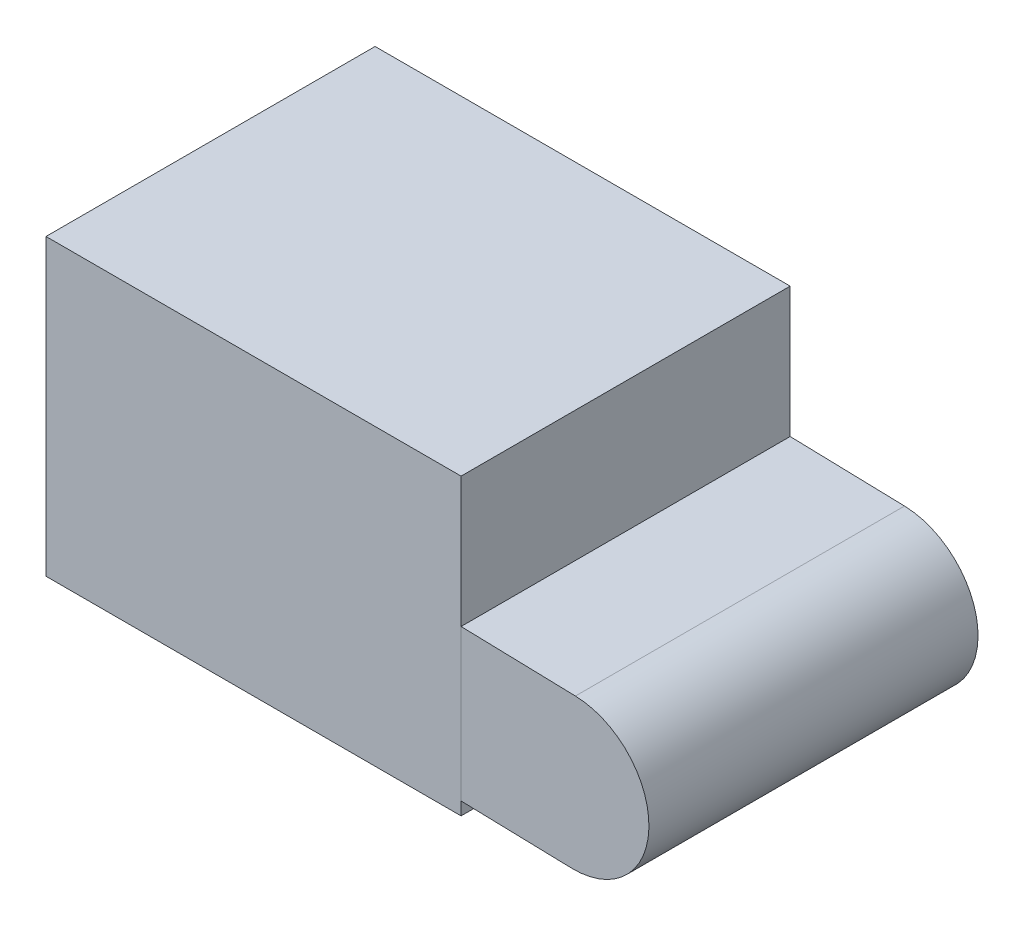
SolidWorks part; units mm, degrees
ref_plane "Front Plane" through (0, 0, 0) normal (0, 0, 1) x (1, 0, 0)
ref_plane "Top Plane" through (0, 0, 0) normal (0, 1, 0) x (1, 0, 0)
ref_plane "Right Plane" through (0, 0, 0) normal (1, 0, 0) x (0, 0, -1)
sketch "Sketch2" plane through (0, 0, 0) normal (0, 0, 1) x (1, 0, 0)
  line L1 (-46.6277, 10.3806) -> (17.6981, 10.3806)
  line L2 (-46.6277, 10.3806) -> (-46.6277, -35.2261)
  line L3 (-46.6277, -35.2261) -> (17.6981, -35.2261)
  line L4 (17.6981, 10.3806) -> (17.6981, -35.2261)
  point P4 (17.6981, -35.2261)
extrude "Boss-Extrude1" add sketch "Sketch2" along normal blind 51
sketch "Sketch3" plane through (0, 0, 0) normal (0, 0, 1) x (1, 0, 0)
  line L0 (35.1077, -21.9747) -> (4.3473, -21.1577) construction
  line L1 (34.797, -33.6745) -> (4.0366, -32.8575)
  line L2 (35.4185, -10.2748) -> (4.6581, -9.4578)
  arc A0 (34.797, -33.6745) -> (35.4185, -10.2748) centre (35.1077, -21.9747) ccw
  arc A1 (4.6581, -9.4578) -> (4.0366, -32.8575) centre (4.3473, -21.1577) ccw
  point P2 (19.7275, -21.5662)
extrude "Boss-Extrude2" add sketch "Sketch3" along normal blind 51 separate body
